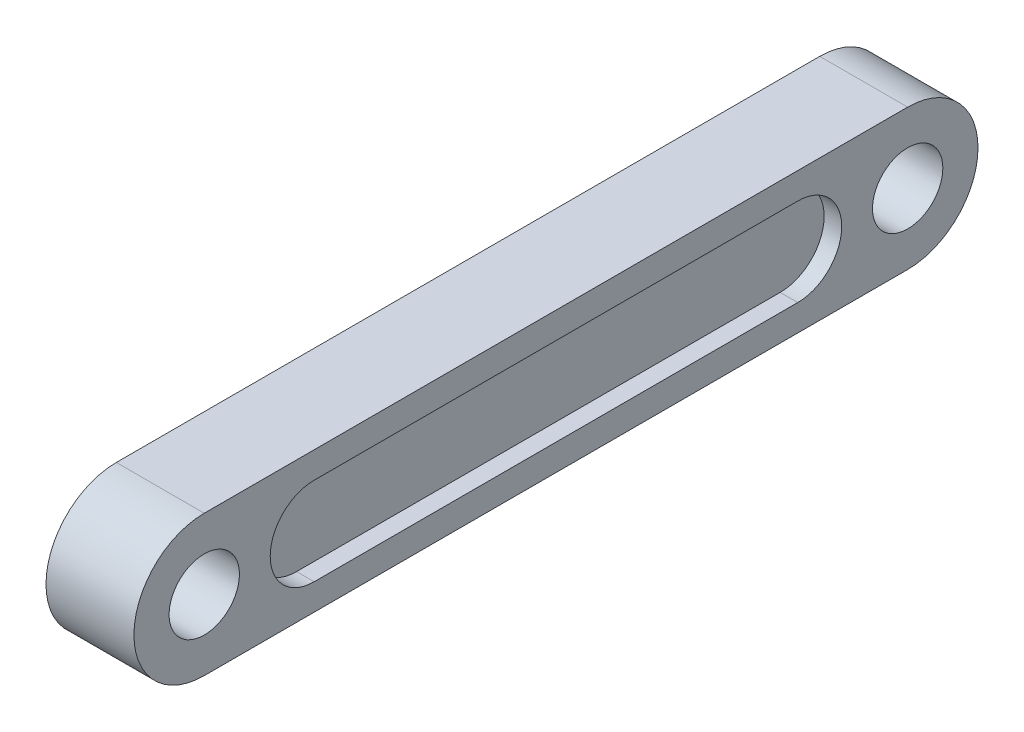
SolidWorks part; units mm, degrees
material "普通碳钢"
ref_plane "前视基准面" through (0, 0, 0) normal (0, 0, 1) x (1, 0, 0)
ref_plane "上视基准面" through (0, 0, 0) normal (0, 1, 0) x (1, 0, 0)
ref_plane "右视基准面" through (0, 0, 0) normal (1, 0, 0) x (0, 0, -1)
sketch "草图1" plane through (0, 0, 0) normal (1, 0, 0) x (0, 0, -1)
  line L0 (-40, 8) -> (40, 8)
  line L1 (-40, -8) -> (40, -8)
  line L2 (0, 0) -> (0, 27.9648) construction
  line L3 (40, 0) -> (0, 0) construction
  line L4 (0, 0) -> (-40, 0) construction
  circle A0 centre (40, 0) radius 4
  arc A1 (-40, -8) -> (-40, 8) centre (-40, 0) cw
  circle A2 centre (-40, 0) radius 4
  arc A3 (40, -8) -> (40, 8) centre (40, 0) ccw
  point P4 (0, 0)
  point P6 (0, -10)
  point P7 (0, 0)
  point P14 (0, 10)
  dimension "D1" = 8
  dimension "D2" = 8
  dimension "D4" = 8
  dimension "D3" = 40
  dimension "D5" = 40
extrude "凸台-拉伸1" add sketch "草图1" along normal mid plane 10
sketch "草图2" plane through (-5, 0, 0) normal (-1, 0, 0) x (0, 0, 1)
  line L0 (-27.5, 0) -> (27.5, 0) construction
  line L1 (-27.5, 5) -> (27.5, 5)
  line L2 (-27.5, -5) -> (27.5, -5)
  arc A0 (-27.5, 5) -> (-27.5, -5) centre (-27.5, 0) ccw
  arc A1 (27.5, -5) -> (27.5, 5) centre (27.5, 0) ccw
  point P3 (0, 0)
  dimension "D2" = 5
  dimension "D1" = 55
extrude "切除-拉伸1" cut sketch "草图2" against normal blind 2
mirror "镜向1" about plane through (0, 0, 0) normal (1, 0, 0) of "切除-拉伸1"
